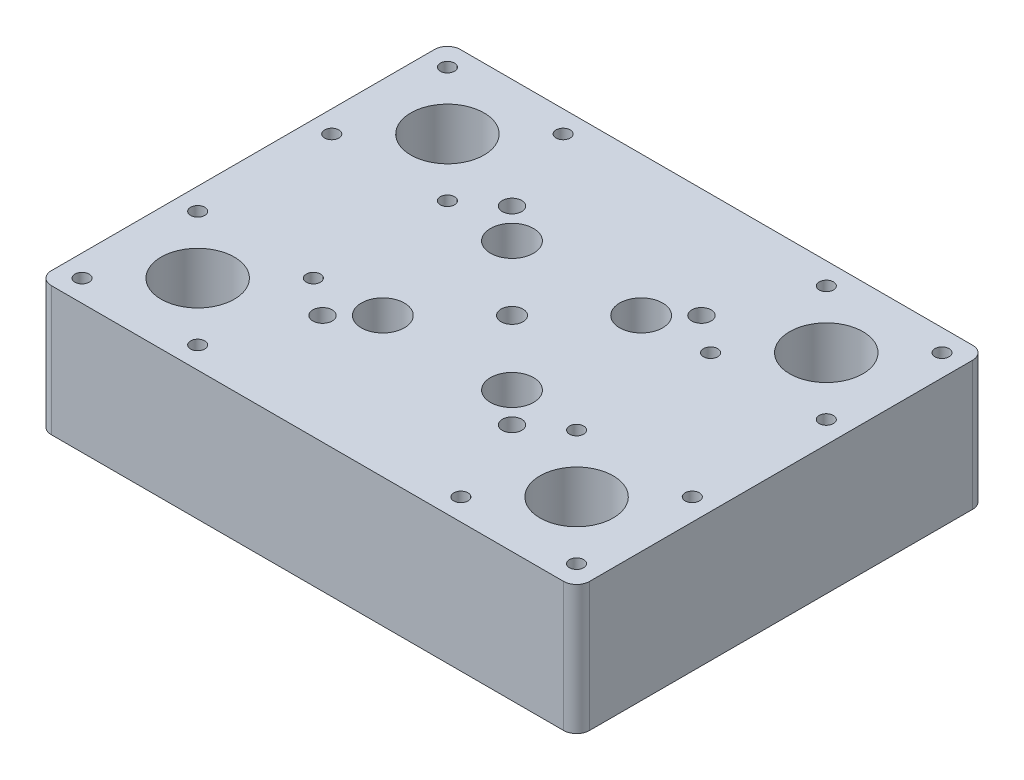
SolidWorks part; units mm, degrees
ref_plane "Front" through (0, 0, 0) normal (0, 0, 1) x (1, 0, 0)
ref_plane "Top" through (0, 0, 0) normal (0, 1, 0) x (1, 0, 0)
ref_plane "Right" through (0, 0, 0) normal (1, 0, 0) x (0, 0, -1)
sketch "Master Sketch" plane through (0, 0, 0) normal (0, 1, 0) x (1, 0, 0)
  line L1 (-62.5, -47.5) -> (62.5, -47.5) construction
  line L2 (-62.5, -47.5) -> (-62.5, 47.5) construction
  line L3 (-62.5, 47.5) -> (62.5, 47.5) construction
  line L4 (62.5, -47.5) -> (62.5, 47.5) construction
  line L5 (0, 47.5) -> (0, -47.5) construction
  line L6 (-62.5, 0) -> (62.5, 0) construction
  line L7 (-25.5, 10.5) -> (-62.5, 10.5) construction
  line L8 (-25.5, 10.5) -> (-25.5, 47.5) construction
  line L9 (-25.5, 47.5) -> (-62.5, 47.5) construction
  line L10 (-62.5, 10.5) -> (-62.5, 47.5) construction
  line L11 (-44, 47.5) -> (-44, 10.5) construction
  line L12 (-25.5, 29) -> (-62.5, 29) construction
  line L13 (25.5, 10.5) -> (62.5, 10.5) construction
  line L14 (25.5, 10.5) -> (25.5, 47.5) construction
  line L15 (25.5, 47.5) -> (62.5, 47.5) construction
  line L16 (62.5, 10.5) -> (62.5, 47.5) construction
  line L17 (44, 47.5) -> (44, 10.5) construction
  line L18 (25.5, 29) -> (62.5, 29) construction
  line L19 (25.5, -10.5) -> (62.5, -10.5) construction
  line L20 (25.5, -10.5) -> (25.5, -47.5) construction
  line L21 (25.5, -47.5) -> (62.5, -47.5) construction
  line L22 (62.5, -10.5) -> (62.5, -47.5) construction
  line L23 (44, -47.5) -> (44, -10.5) construction
  line L24 (25.5, -29) -> (62.5, -29) construction
  line L25 (-25.5, -10.5) -> (-62.5, -10.5) construction
  line L26 (-25.5, -10.5) -> (-25.5, -47.5) construction
  line L27 (-25.5, -47.5) -> (-62.5, -47.5) construction
  line L28 (-62.5, -10.5) -> (-62.5, -47.5) construction
  line L29 (-44, -47.5) -> (-44, -10.5) construction
  line L30 (-25.5, -29) -> (-62.5, -29) construction
  line L31 (-30, -30) -> (30, -30) construction
  line L32 (-30, -30) -> (-30, 30) construction
  line L33 (-30, 30) -> (30, 30) construction
  line L34 (30, -30) -> (30, 30) construction
  line L35 (0, 30) -> (0, -30) construction
  line L36 (-30, 0) -> (30, 0) construction
  circle A0 centre (0, 0) radius 12.5 construction
  circle A1 centre (44, 29) radius 8 construction
  circle A2 centre (44, -29) radius 8 construction
  circle A3 centre (-44, -29) radius 8 construction
  circle A4 centre (-44, 29) radius 8 construction
  point P0 (0, 0)
  dimension "D3" = 25
  dimension "D4" = 16
  dimension "D1" = 125
  dimension "D2" = 95
  dimension "D5" = 37
  dimension "D6" = 60
sketch "Sketch1" plane through (0, 0, 0) normal (0, 1, 0) x (1, 0, 0)
  line L0 (44, -47.5) -> (44, -10.5) construction
  line L1 (-62.5, 47.5) -> (62.5, 47.5)
  line L2 (-62.5, 47.5) -> (-62.5, -47.5)
  line L3 (-62.5, -47.5) -> (62.5, -47.5)
  line L4 (62.5, 47.5) -> (62.5, -47.5)
  circle A0 centre (-44, 29) radius 8.5
  circle A1 centre (44, 29) radius 8.5
  circle A2 centre (44, -29) radius 8.5
  circle A3 centre (-44, -29) radius 8.5
  dimension "D1" = 17
extrude "Boss-Extrude1" add sketch "Sketch1" along normal blind 30
hole_wizard "M4x0.7 Tapped Hole1" positions "Sketch3" profile "Sketch2" tap size "M4x0.7" standard "ANSI Metric"
sketch "Sketch3" plane through (0, 30, 0) normal (0, 1, 0) x (1, 0, 0)
  line L0 (-57.435, 15.565) -> (-44, 29) construction
  line L1 (-25.5, 29) -> (-62.5, 29) construction
  line L3 (-44, 47.5) -> (-44, 10.5) construction
  line L4 (-57.435, 42.435) -> (-44, 29) construction
  line L5 (-44, 29) -> (-30.565, 15.565) construction
  line L7 (-30.565, 42.435) -> (-44, 29) construction
  point P0 (-57.435, 42.435)
  point P2 (-30.565, 42.435)
  point P4 (-30.565, 15.565)
  point P6 (-57.435, 15.565)
  dimension "D1" = 19
sketch "Sketch2" plane through (-57.435, 30, -42.435) normal (1, 0, 0) x (0, 0, 1)
  line L0 (0, 0) -> (0, 8.9914)
  line L1 (0, 8.9914) -> (1.65, 8)
  line L2 (1.65, 8) -> (1.65, 0)
  line L5 (1.65, 0) -> (0, 0)
  line L10 (0, 8.9914) -> (-1.65, 8) construction
  line L11 (0, -6.35) -> (0, 107.95) construction
  dimension "Tap Drill Dia." = 3.3
  dimension "Tap Drill Depth" = 8
  dimension "Drill Angle" = 118
cosmetic thread "Hole Thread1" parameters "D1"=6, "D2"=4
cosmetic thread "Hole Thread2" parameters "D1"=6, "D2"=4
cosmetic thread "Hole Thread3" parameters "D1"=6, "D2"=4
cosmetic thread "Hole Thread4" parameters "D1"=6, "D2"=4
pattern_linear "LPattern1" count 2 spacing 88 along (1, 0, 0) count 2 spacing 58 along (0, 0, 1) of "M4x0.7 Tapped Hole1"
sketch "Sketch5" plane through (0, 0, 0) normal (0, -1, 0) x (1, 0, 0)
  line L1 (-30, 30) -> (30, 30)
  line L2 (-30, 30) -> (-30, -30)
  line L3 (-30, -30) -> (30, -30)
  line L4 (30, 30) -> (30, -30)
extrude "Cut-Extrude1" cut sketch "Sketch5" against normal blind 20
fillet "Fillet1" radius 7 4 edges at (30, 10, -30) (30, 10, 30) (-30, 10, -30) (-30, 10, 30)
fillet "Fillet2" radius 3 4 edges at (62.5, 15, -47.5) (62.5, 15, 47.5) (-62.5, 15, 47.5) (-62.5, 15, -47.5)
hole_wizard "1/4-20 Tapped Hole1" positions "Sketch7" profile "Sketch6" tap size "1/4-20" standard "ANSI Inch" end condition through all
sketch "Sketch7" plane through (0, 20, 0) normal (0, -1, 0) x (-1, 0, 0)
  point P0 (0, 0)
sketch "Sketch6" plane through (0, 20, 0) normal (1, 0, 0) x (0, 0, -1)
  line L0 (0, 0) -> (0, 10)
  line L1 (0, 10) -> (2.5527, 10)
  line L2 (2.5527, 10) -> (2.5527, 0)
  line L5 (2.5527, 0) -> (0, 0)
  line L11 (0, -6.35) -> (0, 107.95) construction
  dimension "Thru Tap Drill Dia." = 5.1054
  dimension "Thru Tap Drill Depth" = 10
cosmetic thread "Hole Thread5" parameters "D2"=6.35
sketch "Sketch8" plane through (0, 0, 0) normal (0, -1, 0) x (1, 0, 0)
  circle A0 centre (-15, 15) radius 5
  circle A1 centre (-15, -15) radius 5
  circle A2 centre (15, 15) radius 5
  circle A3 centre (15, -15) radius 5
  dimension "D1" = 10
  dimension "D2" = 15
  dimension "D3" = 15
  dimension "D4" = 15
  dimension "D5" = 15
extrude "Cut-Extrude2" cut sketch "Sketch8" against normal through all
hole_wizard "M4 Clearance Hole1" positions "Sketch10" profile "Sketch11" hole size "M4" standard "ANSI Metric" end condition through all
sketch "Sketch10" plane through (0, 20, 0) normal (0, -1, 0) x (-1, 0, 0)
  point P0 (22, -22)
  point P2 (-22, -22)
  point P4 (-22, 22)
  point P6 (22, 22)
  dimension "D1" = 22
  dimension "D2" = 22
  dimension "D3" = 22
  dimension "D4" = 22
sketch "Sketch11" plane through (-22, 20, 22) normal (1, 0, 0) x (0, 0, -1)
  line L0 (0, 0) -> (0, 10)
  line L1 (0, 10) -> (2.25, 10)
  line L2 (2.25, 10) -> (2.25, 0)
  line L5 (2.25, 0) -> (0, 0)
  line L11 (0, -6.35) -> (0, 107.95) construction
  dimension "Thru Hole Dia." = 4.5
  dimension "Thru Hole Depth" = 10
